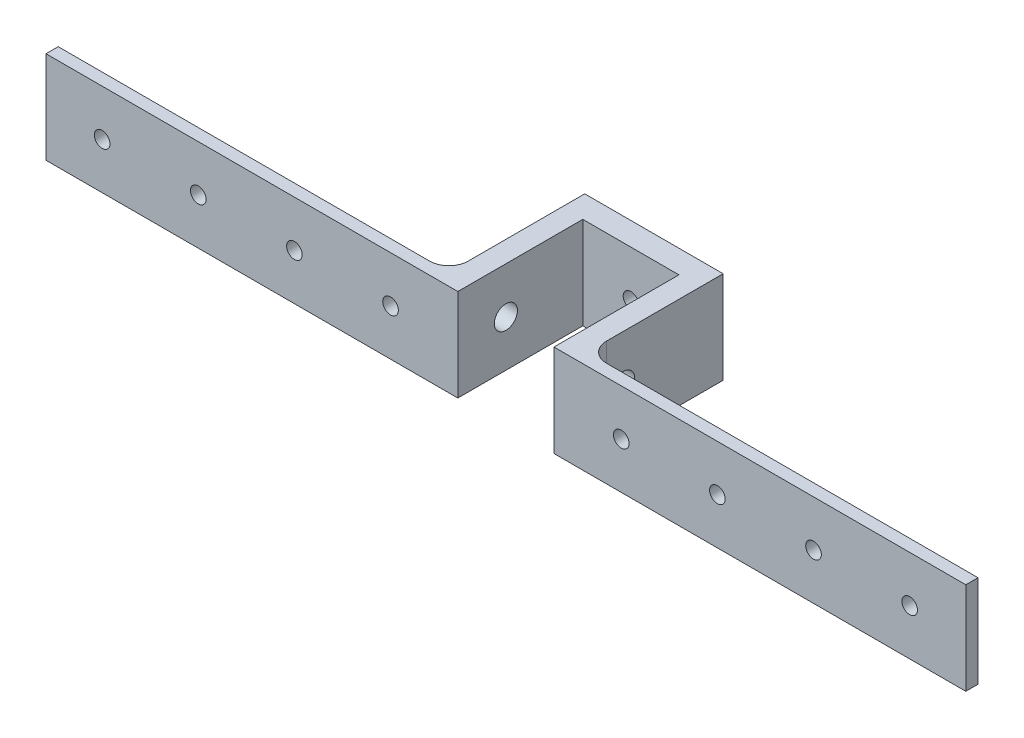
SolidWorks part; units mm, degrees
ref_plane "Front Plane" through (0, 0, 0) normal (0, 0, 1) x (1, 0, 0)
ref_plane "Top Plane" through (0, 0, 0) normal (0, 1, 0) x (1, 0, 0)
ref_plane "Right Plane" through (0, 0, 0) normal (1, 0, 0) x (0, 0, -1)
sketch "Sketch1" plane through (0, 0, 0) normal (0, 1, 0) x (1, 0, 0)
  line L0 (-18, -16.134) -> (-12.5, -16.134)
  line L1 (12.5, -16.134) -> (-12.5, -16.134)
  line L2 (12.5, -16.134) -> (12.5, 16.366)
  line L3 (12.5, 16.366) -> (-12.5, 16.366)
  line L4 (-12.5, -16.134) -> (-12.5, 16.366)
  line L5 (-11.962, -16.134) -> (11.738, -16.134) construction
  line L8 (18, -16.134) -> (18, 22.366)
  line L9 (18, 22.366) -> (-18, 22.366)
  line L10 (-18, -16.134) -> (-18, 22.366)
  line L13 (12.5, -16.134) -> (18, -16.134)
  point P0 (0, 0)
  point P6 (0, 0)
  dimension "D1" = 25
  dimension "D2" = 36
  dimension "D3" = 5.5
  dimension "D4" = 12.5
  dimension "D6" = 6
  dimension "D7" = 22.366
extrude "Boss-Extrude1" add sketch "Sketch1" along normal blind 24 contours L2 L13 L8 L9 L10 L0 L4 L3
sketch "Sketch2" plane through (0, 0, -22.366) normal (0, 0, -1) x (-1, 0, 0)
  line L0 (-18, 12) -> (18, 12) construction
  line L1 (-18, 24) -> (-18, 0) construction
  line L2 (18, 24) -> (18, 0) construction
  line L3 (0, 24) -> (0, 0) construction
  line L4 (-18, 24) -> (18, 24) construction
  circle A0 centre (0, 12) radius 2
  dimension "D1" = 4
extrude "Cut-Extrude1" cut sketch "Sketch2" against normal blind 24
sketch "Sketch3" plane through (-18, 0, 0) normal (-1, 0, 0) x (0, 0, 1)
  line L0 (-22.366, 12) -> (16.134, 12) construction
  line L1 (-22.366, 24) -> (-22.366, 0) construction
  line L2 (16.134, 24) -> (16.134, 0) construction
  circle A0 centre (3.634, 12) radius 3
  dimension "D2" = 6
  dimension "D1" = 26
extrude "Cut-Extrude2" cut sketch "Sketch3" against normal through all both and the other way through all
sketch "Sketch4" plane through (-18, 0, 0) normal (-1, 0, 0) x (0, 0, 1)
  line L0 (16.134, 24) -> (-22.366, 24) construction
  line L1 (16.134, 0) -> (12.959, 0)
  line L2 (16.134, 0) -> (16.134, 24)
  line L3 (16.134, 24) -> (12.959, 24)
  line L4 (12.959, 0) -> (12.959, 24)
  line L5 (16.134, 0) -> (-22.366, 0) construction
  dimension "D1" = 3.175
extrude "Boss-Extrude2" add sketch "Sketch4" along normal blind 101.6
sketch "Sketch7" plane through (0, 0, 12.959) normal (0, 0, -1) x (-1, 0, 0)
  line L0 (119.6, 12) -> (18, 12) construction
  line L1 (119.6, 0) -> (18, 0) construction
  line L2 (119.6, 0) -> (119.6, 24) construction
  line L3 (119.6, 24) -> (18, 24) construction
  line L4 (18, 0) -> (18, 24) construction
  circle A0 centre (30, 12) radius 2.032
  circle A1 centre (55, 12) radius 2.032
  circle A2 centre (80, 12) radius 2.032
  circle A3 centre (105, 12) radius 2.032
  circle A4 centre (130, 12) radius 2.032
  circle A5 centre (155, 12) radius 2.032
  dimension "D3" = 4.064
  dimension "D1" = 12
  dimension "D2" = 6
extrude "Cut-Extrude3" cut sketch "Sketch7" against normal through all
ref_plane "Plane1" through (0, 0, 0) normal (-1, 0, 0) x (0, 0, 1)
mirror "Mirror1" about plane through (0, 0, 0) normal (-1, 0, 0) of "Cut-Extrude3", "Boss-Extrude2"
fillet "Fillet1" radius 5 1 edges at (-18, 12, 12.959)
fillet "Fillet2" radius 5 1 edges at (18, 12, 12.959)
equation "\"D1@Boss-Extrude2\"=6in"
equation "\"D3@Sketch7\"=.16in"
